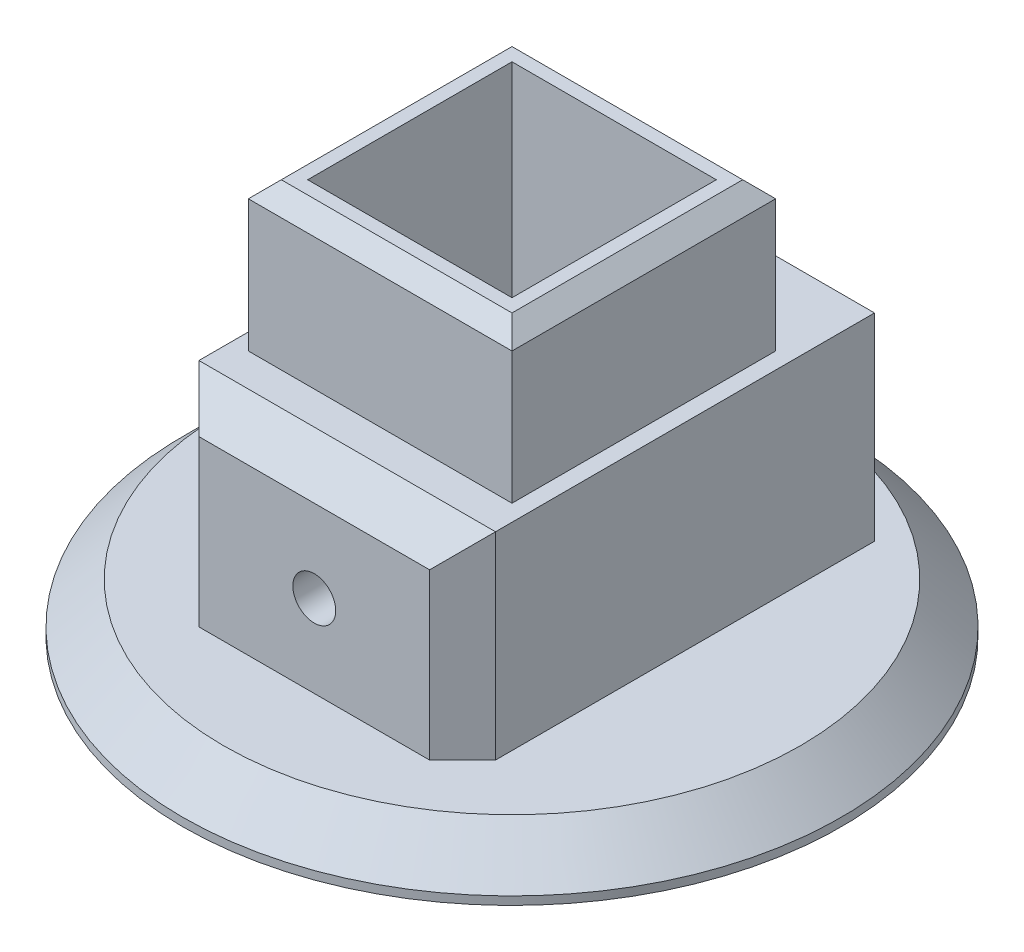
SolidWorks part; units mm, degrees
ref_plane "Front Plane" through (0, 0, 0) normal (0, 0, 1) x (1, 0, 0)
ref_plane "Top Plane" through (0, 0, 0) normal (0, 1, 0) x (1, 0, 0)
ref_plane "Right Plane" through (0, 0, 0) normal (1, 0, 0) x (0, 0, -1)
sketch "Sketch1" plane through (0, 0, 0) normal (0, 1, 0) x (1, 0, 0)
  line L0 (0, 16) -> (0, 0) construction
  line L1 (-8, 16) -> (8, 16)
  line L2 (-8, 16) -> (-8, 0)
  line L10 (8, 16) -> (8, 0)
  line L11 (-8, 0) -> (8, 0)
  dimension "D1" = 16
  dimension "D2" = 16
extrude "Boss-Extrude1" add sketch "Sketch1" along normal blind 24
sketch "Sketch12" plane through (0, 24, 0) normal (0, 1, 0) x (1, 0, 0)
  line L1 (-6.2, 14.2) -> (6.2, 14.2)
  line L2 (-6.2, 14.2) -> (-6.2, 1.8)
  line L3 (-6.2, 1.8) -> (6.2, 1.8)
  line L4 (6.2, 14.2) -> (6.2, 1.8)
  line L5 (0, 0) -> (0, 16) construction
  line L6 (8, 8) -> (-13.65, 8) construction
  line L7 (8, 16) -> (8, 0) construction
  dimension "D1" = 12.4
  dimension "D2" = 12.4
extrude "Cut-Extrude6" cut sketch "Sketch12" against normal offset from surface (22 mm away) 2 up to face at (0, 0, -8)
sketch "Sketch13" plane through (0, 0, 0) normal (0, 1, 0) x (1, 0, 0)
  line L0 (0, 16) -> (0, 0) construction
  circle A0 centre (0, 8) radius 20
  dimension "D1" = 40
extrude "Boss-Extrude2" add sketch "Sketch13" along normal blind 3
chamfer "Chamfer1" distance 2.5 angle 45 1 edges at (0, 3, 12)
sketch "Sketch14" plane through (0, 3, 0) normal (0, 1, 0) x (1, 0, 0)
  line L1 (-8, 16) -> (8, 16)
  line L3 (-8, 23) -> (8, 23)
  line L5 (-8, 0) -> (8, 0)
  line L7 (-8, -4) -> (8, -4)
  line L9 (0, 0) -> (0, 24.5816) construction
  line L10 (-8, 23) -> (-9, 23)
  line L11 (-8, 16) -> (-8, 0)
  line L12 (-8, -4) -> (-9, -4)
  line L13 (-9, 23) -> (-9, -4)
  line L14 (8, -4) -> (9, -4)
  line L15 (8, 23) -> (9, 23)
  line L16 (9, 23) -> (9, -4)
  line L17 (8, 16) -> (8, 0) construction
  line L18 (8, 16) -> (8, 0)
  dimension "D1" = 7
  dimension "D2" = 4
  dimension "D3" = 1
extrude "Boss-Extrude3" add sketch "Sketch14" along normal blind 12
sketch "Sketch5" plane through (0, 0, -23) normal (0, 0, -1) x (-1, 0, 0)
  line L0 (0, 24) -> (0, 0) construction
  line L3 (-22.5, 8) -> (22.5, 8) construction
  line L4 (-2.1, 11.1) -> (2.1, 11.1)
  line L5 (-3.1, 10.1) -> (-3.1, 8.8)
  line L6 (-3.1, 4.9) -> (3.1, 4.9)
  line L7 (3.1, 10.1) -> (3.1, 8.8)
  line L10 (-2.1, 11.1) -> (-3.1, 10.1)
  line L11 (2.1, 11.1) -> (3.1, 10.1)
  line L12 (-3.1, 7.2) -> (-3.1, 4.9)
  line L13 (3.1, 7.2) -> (3.1, 4.9)
  line L14 (-8, 24) -> (8, 24) construction
  arc A0 (-3.1, 8.8) -> (-3.1, 7.2) centre (-3.1, 8) ccw
  arc A1 (3.1, 8.8) -> (3.1, 7.2) centre (3.1, 8) cw
  point P6 (-3.1, 11.1)
  dimension "D4" = 0.8
  dimension "D1" = 8
  dimension "D2" = 6.2
  dimension "D3" = 6.2
extrude "Cut-Extrude1" cut sketch "Sketch5" against normal blind 7.5
sketch "Sketch11" plane through (0, 11.1, 0) normal (0, -1, 0) x (1, 0, 0)
  line L0 (2.1, -15.5) -> (2.1, -23) construction
  line L1 (-2.1, -15.5) -> (2.1, -15.5)
  line L2 (-2.1, -15.5) -> (-2.1, -21)
  line L3 (-2.1, -21) -> (2.1, -21)
  line L4 (2.1, -15.5) -> (2.1, -21)
  line L6 (22.5, -23) -> (-22.5, -23) construction
  dimension "D1" = 2
extrude "Cut-Extrude5" cut sketch "Sketch11" against normal blind 0.1 and the other way blind 6.3
chamfer "Chamfer2" distance 2 angle 45 3 edges at (-9, 9, -23) (9, 9, -23) (0, 15, -23)
chamfer "Chamfer4" distance 2 angle 45 3 edges at (0, 15, 4) (9, 9, 4) (-9, 9, 4)
sketch "Sketch15" plane through (0, 0, -15.5) normal (0, 0, -1) x (-1, 0, 0)
  line L0 (-22.5, 8) -> (22.5, 8) construction
  circle A0 centre (0, 8) radius 1.3
  dimension "D1" = 2.6
extrude "Cut-Extrude7" cut sketch "Sketch15" against normal through all
chamfer "Chamfer5" distance 1 angle 45 4 edges at (0, 24, 0) (-8, 24, -8) (0, 24, -16) (8, 24, -8)
